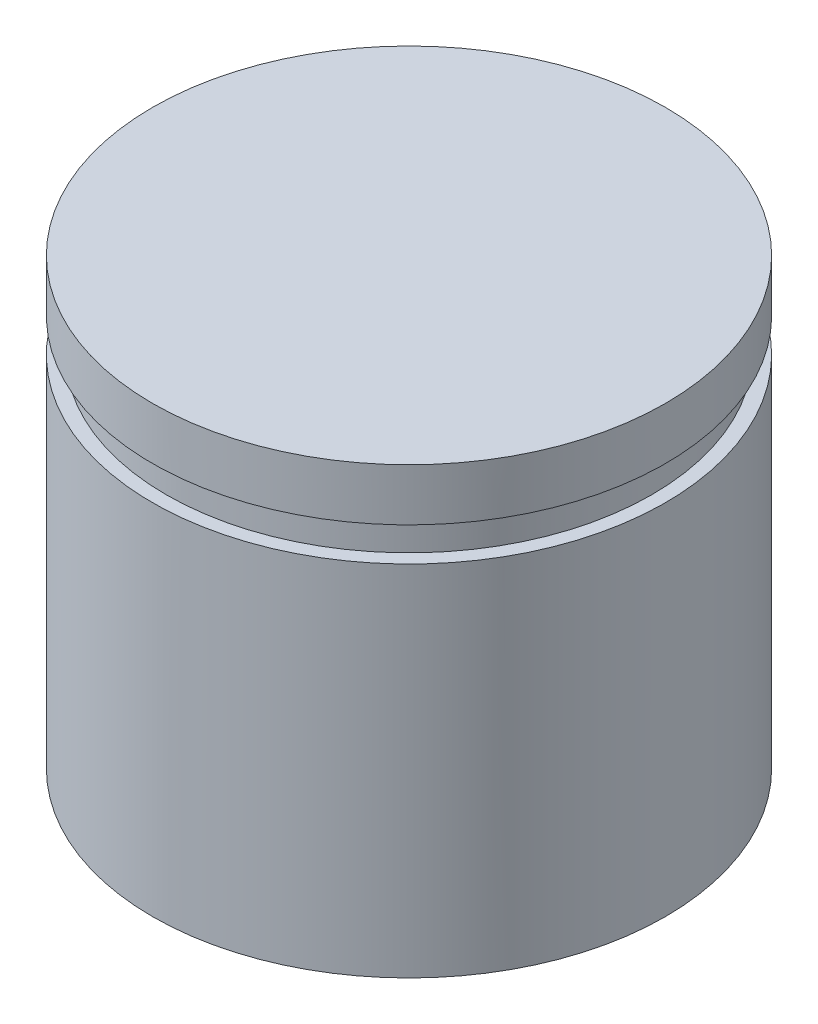
SolidWorks part; units mm, degrees
material "AISI 1020"
ref_plane "Front Plane" through (0, 0, 0) normal (0, 0, 1) x (1, 0, 0)
ref_plane "Top Plane" through (0, 0, 0) normal (0, 1, 0) x (1, 0, 0)
ref_plane "Right Plane" through (0, 0, 0) normal (1, 0, 0) x (0, 0, -1)
sketch "Sketch1" plane through (0, 0, 0) normal (0, 1, 0) x (1, 0, 0)
  circle A0 centre (0, 0) radius 7.5
extrude "Boss-Extrude1" add sketch "Sketch1" along normal blind 13
ref_plane "Plane1" through (0, 11.476, 0) normal (0, 1, 0) x (1, 0, 0)
sketch "Sketch2" plane through (0, 11.476, 0) normal (0, 1, 0) x (1, 0, 0)
  line L0 (-10.5373, 10.4835) -> (-10.8605, -10.9502)
  line L1 (-10.8605, -10.9502) -> (14.2712, -10.9502)
  line L2 (14.2712, -10.9502) -> (12.4402, 11.5246)
  line L3 (12.4402, 11.5246) -> (-10.5373, 10.4835)
  circle A0 centre (0, 0) radius 7.0993
  dimension "D1" = 14.1986
extrude "Cut-Extrude1" cut sketch "Sketch2" against normal blind 0.9906
